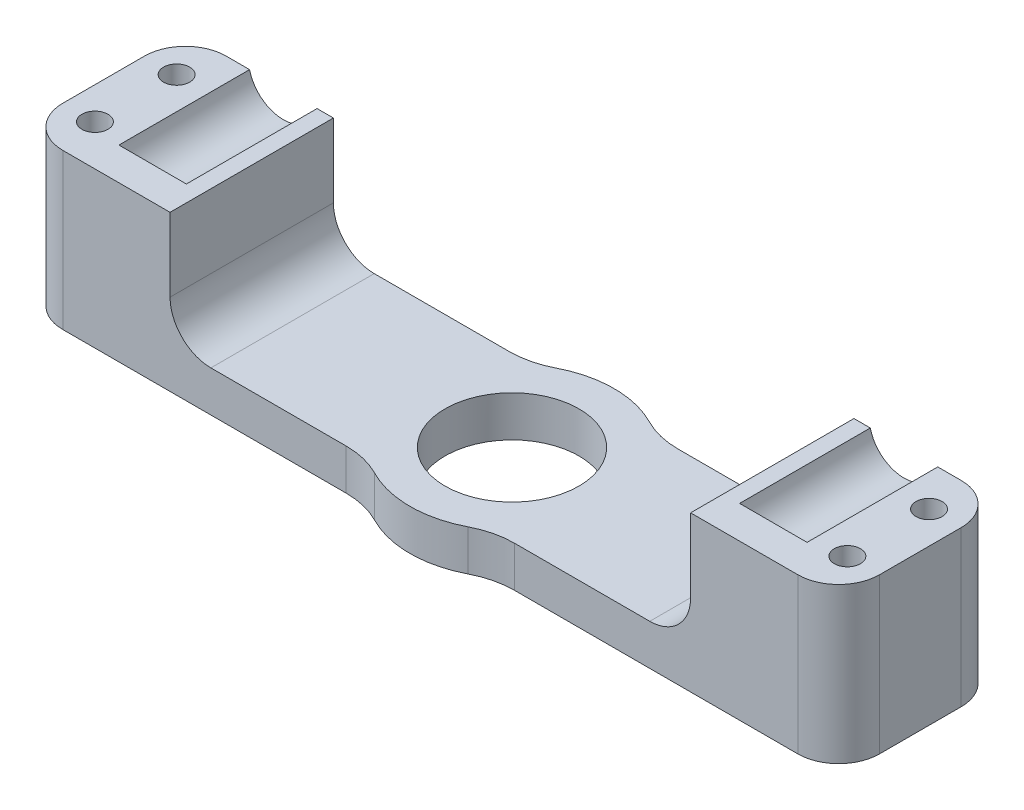
SolidWorks part; units mm, degrees
ref_plane "Front Plane" through (0, 0, 0) normal (0, 0, 1) x (1, 0, 0)
ref_plane "Top Plane" through (0, 0, 0) normal (0, 1, 0) x (1, 0, 0)
ref_plane "Right Plane" through (0, 0, 0) normal (1, 0, 0) x (0, 0, -1)
sketch "Sketch1" plane through (0, 0, 0) normal (0, 1, 0) x (1, 0, 0)
  line L0 (-44, 0) -> (-44, -44) construction
  line L1 (-44, -44) -> (44, -44) construction
  line L2 (44, -44) -> (44, 0) construction
  line L4 (-44, -10) -> (44, -10)
  line L5 (-44, -10) -> (-44, 10)
  line L6 (-44, 10) -> (44, 10)
  line L7 (44, -10) -> (44, 10)
  line L8 (-44, -10) -> (44, 10) construction
  line L9 (-44, 10) -> (44, -10) construction
  arc A0 (44, 0) -> (-44, 0) centre (0, 0) ccw construction
  dimension "D1" = 88
  dimension "D2" = 88
  dimension "D3" = 20
extrude "Boss-Extrude1" add sketch "Sketch1" along normal blind 40
sketch "Sketch2" plane through (0, 0, 10) normal (0, 0, 1) x (1, 0, 0)
  line L1 (-1044, 20) -> (48956, 20) construction
  line L2 (0, -1000) -> (0, 49000) construction
  line L3 (-44, 40) -> (-44, 0) construction
  circle A0 centre (-38, 20) radius 4.25
  circle A1 centre (38, 20) radius 4.25
  point P2 (-44, 20)
  dimension "D1" = 8.5
  dimension "D2" = 6
extrude "Cut-Extrude1" cut sketch "Sketch2" against normal through all
sketch "Sketch7" plane through (0, 40, 0) normal (0, 1, 0) x (1, 0, 0)
  circle A0 centre (0, 0) radius 12.5
  dimension "D1" = 25
extrude "Boss-Extrude2" add sketch "Sketch7" against normal up to surface (40 mm away) up to face at (0, 0, 0)
sketch "Sketch4" plane through (0, 40, 0) normal (0, 1, 0) x (1, 0, 0)
  circle A0 centre (0, 0) radius 8.2
  dimension "D1" = 16.4
extrude "Cut-Extrude3" cut sketch "Sketch4" against normal through all
fillet "Fillet2" radius 10 4 edges at (-7.5, 20, 10) (7.5, 20, 10) (7.5, 20, -10) (-7.5, 20, -10)
sketch "Sketch9" plane through (-44, 0, 0) normal (-1, 0, 0) x (0, 0, 1)
  line L5 (-1017.3065, 40) -> (48982.6935, 40) construction
  line L6 (-1016.9067, 19) -> (48983.0933, 19) construction
  line L7 (-12.5, 40) -> (-12.5, 0) construction
  line L8 (-10, 40) -> (10, 40) construction
  line L9 (12.5, 0) -> (12.5, 40) construction
  line L10 (-13.5, 40) -> (13.5, 40)
  line L11 (-13.5, 40) -> (-13.5, 19)
  line L12 (-13.5, 19) -> (13.5, 19)
  line L13 (13.5, 40) -> (13.5, 19)
  line L14 (-12.5, 40) -> (-12.5, 0) construction
  point P3 (-12.5, 19)
  point P21 (-12.5, 20)
  dimension "D1" = 1
  dimension "D2" = 1
  dimension "D3" = 1
extrude "Cut-Extrude4" cut sketch "Sketch9" against normal through all
sketch "Sketch10" plane through (0, 0, 0) normal (0, 0, 1) x (1, 0, 0)
  line L0 (44, 0) -> (10.3078, 0) construction
  line L1 (31.8693, 21) -> (-31.8693, 21)
  line L2 (31.8693, 21) -> (31.8693, 5)
  line L3 (31.8693, 5) -> (-31.8693, 5)
  line L4 (-31.8693, 21) -> (-31.8693, 5)
  line L5 (10.3078, 19) -> (33.8693, 19) construction
  dimension "D1" = 5
  dimension "D2" = 2
  dimension "D3" = 2
  dimension "D4" = 2
extrude "Cut-Extrude5" cut sketch "Sketch10" against normal through all and the other way through all
fillet "Fillet3" radius 5 2 edges at (-31.8693, 5, 0) (31.8693, 5, 0)
sketch "Sketch11" plane through (44, 0, 0) normal (1, 0, 0) x (0, 0, -1)
  line L4 (10, 0) -> (10, 19)
  line L5 (10, 19) -> (-10, 19)
  line L6 (-10, 19) -> (-10, 0)
  line L7 (-10, 0) -> (10, 0)
  line L8 (10, 0) -> (10, 19)
  line L9 (10, 19) -> (-10, 19)
  line L10 (-10, 19) -> (-10, 0)
  line L11 (-10, 0) -> (10, 0)
  dimension "D1" = 0
extrude "Boss-Extrude3" add sketch "Sketch11" along normal blind 6
sketch "Sketch12" plane through (0, 19, 0) normal (0, 1, 0) x (1, 0, 0)
  line L0 (50, -10) -> (42.1307, -10) construction
  line L1 (42.1307, 10) -> (50, 10) construction
  circle A0 centre (46.0653, 5) radius 1.6
  circle A1 centre (46.0653, -5) radius 1.6
  point P4 (46.0653, -10)
  dimension "D1" = 3.2
  dimension "D2" = 5
  dimension "D3" = 5
extrude "Cut-Extrude6" cut sketch "Sketch12" against normal through all
mirror "Mirror1" about plane through (0, 0, 0) normal (1, 0, 0) of "Cut-Extrude6", "Boss-Extrude3"
fillet "Fillet5" radius 5 4 edges at (-50, 9.5, -10) (-50, 9.5, 10) (50, 9.5, 10) (50, 9.5, -10)
sketch "Sketch13" plane through (0, 0, 10) normal (0, 0, 1) x (1, 0, 0)
  line L0 (-42.1307, 19) -> (-33.8693, 19)
  line L1 (33.8693, 19) -> (42.1307, 19)
  arc A0 (33.8693, 19) -> (42.1307, 19) centre (38, 20) ccw construction
  arc A1 (33.8693, 19) -> (42.1307, 19) centre (38, 20) ccw
  arc A2 (-42.1307, 19) -> (-33.8693, 19) centre (-38, 20) ccw construction
  arc A3 (-42.1307, 19) -> (-33.8693, 19) centre (-38, 20) ccw
extrude "Boss-Extrude4" add sketch "Sketch13" against normal blind 4
